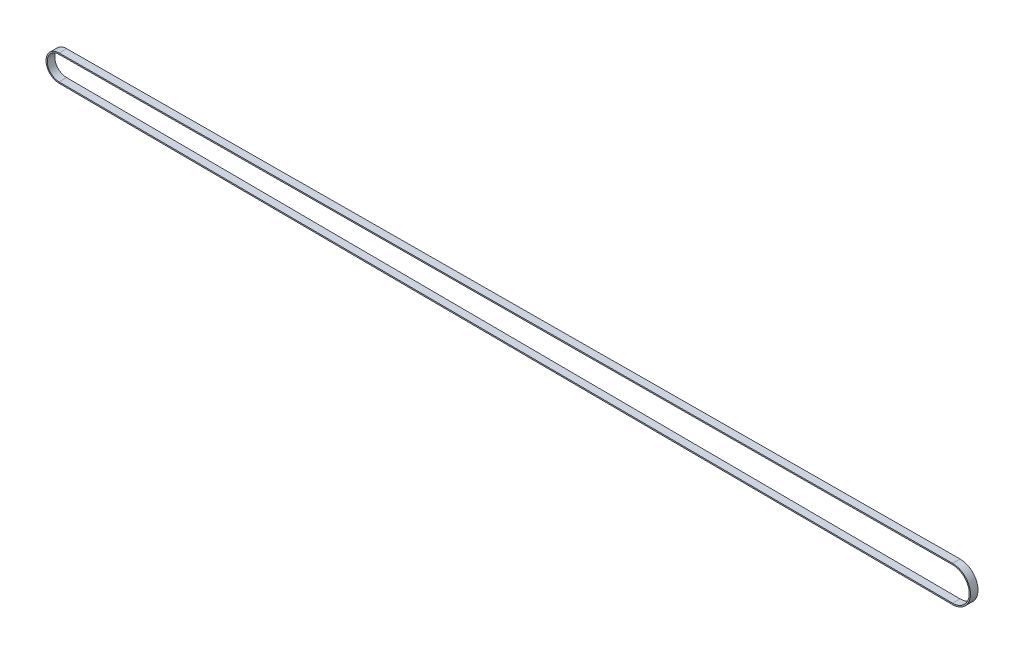
SolidWorks part; units mm, degrees
ref_plane "Plan de face" through (0, 0, 0) normal (0, 0, 1) x (1, 0, 0)
ref_plane "Plan de dessus" through (0, 0, 0) normal (0, 1, 0) x (1, 0, 0)
ref_plane "Plan de droite" through (0, 0, 0) normal (1, 0, 0) x (0, 0, -1)
sketch "Esquisse2" plane through (0, 0, 331.0565) normal (0, 0, 1) x (1, 0, 0)
  line L0 (0, 0) -> (1, 0) construction
  line L1 (0, 0) -> (0, 1) construction
  line L4 (-6.1042, -10.1383) -> (-363.0941, -8.2384)
  line L5 (-363.0941, 1.2615) -> (-6.1042, 3.1615)
  arc A0 (-6.1042, 3.1615) -> (-6.1042, -10.1383) centre (-6.0688, -3.4884) cw
  arc A2 (-363.0941, -8.2384) -> (-363.0941, 1.2615) centre (-363.0688, -3.4884) cw
extrude "Extru.-Mince1" add sketch "Esquisse2" against normal blind 3 thin thin type one direction wall 0.5
